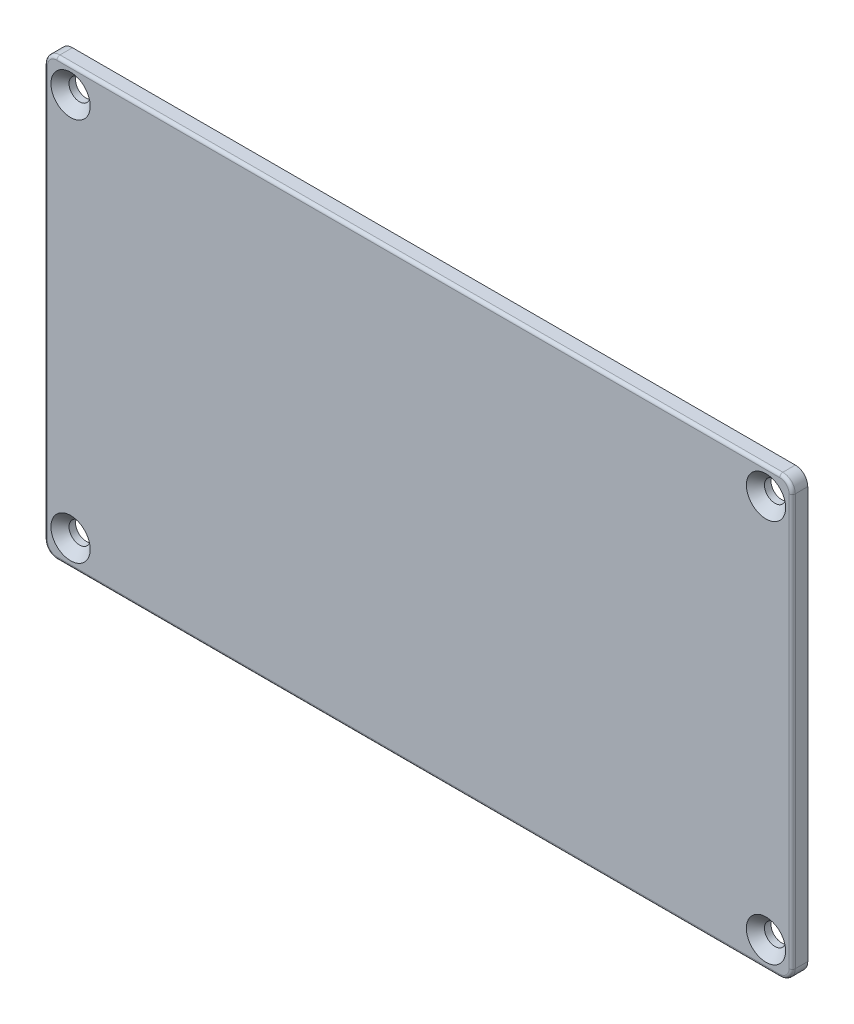
SolidWorks part; units mm, degrees
ref_plane "Front Plane" through (0, 0, 0) normal (0, 0, 1) x (1, 0, 0)
ref_plane "Top Plane" through (0, 0, 0) normal (0, 1, 0) x (1, 0, 0)
ref_plane "Right Plane" through (0, 0, 0) normal (1, 0, 0) x (0, 0, -1)
sketch "Sketch1" plane through (0, 0, 0) normal (0, 0, 1) x (1, 0, 0)
  line L1 (60, -35) -> (-60, -35)
  line L2 (60, -35) -> (60, 35)
  line L3 (60, 35) -> (-60, 35)
  line L4 (-60, -35) -> (-60, 35)
  line L5 (60, -35) -> (-60, 35) construction
  line L6 (60, 35) -> (-60, -35) construction
  point P0 (0, 0)
extrude "Boss-Extrude1" add sketch "Sketch1" along normal blind 2.5
fillet "Fillet1" radius 2 4 edges at (60, -35, 1.25) (-60, -35, 1.25) (-60, 35, 1.25) (60, 35, 1.25)
sketch "Sketch2" plane through (0, 0, 2.5) normal (0, 0, 1) x (1, 0, 0)
  line L0 (58, 35) -> (-58, 35) construction
  line L1 (-60, 33) -> (-60, -33) construction
  line L2 (-58, -35) -> (58, -35) construction
  line L3 (60, -33) -> (60, 33) construction
  circle A0 centre (-55.8, 30.8) radius 1.5
  circle A1 centre (55.8, 30.8) radius 1.5
  circle A2 centre (55.8, -30.8) radius 1.5
  circle A3 centre (-55.8, -30.8) radius 1.5
  dimension "D1" = 4.2
  dimension "D2" = 4.2
  dimension "D3" = 3
  dimension "D4" = 4.2
  dimension "D5" = 4.2
  dimension "D6" = 4.2
  dimension "D7" = 4.2
  dimension "D8" = 4.2
  dimension "D9" = 4.2
hole_wizard "CSK for M3 Countersunk Flat Head Screw1" positions "3DSketch1" profile "Sketch3" countersink size "M3" standard "ISO"
sketch3d "3DSketch1"
  point P0 (-55.8, 30.8, 2.5)
  point P3 (55.8, 30.8, 2.5)
  point P6 (55.8, -30.8, 2.5)
  point P9 (-55.8, -30.8, 2.5)
sketch "Sketch3" plane through (-55.8, 30.8, 2.5) normal (1, 0, 0) x (0, -1, 0)
  line L0 (0, 0) -> (0, 11.0215)
  line L1 (0, 11.0215) -> (1.7, 10)
  line L2 (1.7, 10) -> (1.7, 1.45)
  line L3 (1.7, 1.45) -> (3.15, 0)
  line L5 (3.15, 0) -> (0, 0)
  line L6 (-1.7, 1.45) -> (-3.15, 0) construction
  line L10 (0, 11.0215) -> (-1.7, 10) construction
  line L11 (0, -6.35) -> (0, 107.95) construction
  dimension "Hole Dia." = 3.4
  dimension "Hole Depth" = 10
  dimension "Near C'Sink Dia." = 6.3
  dimension "Near C'Sink Angle" = 90
  dimension "Drill Angle" = 118
fillet "Fillet2" radius 0.5 8 edges at (-59.4142, 34.4142, 2.5) (0, 35, 2.5) (59.4142, 34.4142, 2.5) (60, 0, 2.5) (59.4142, -34.4142, 2.5) (0, -35, 2.5) (-59.4142, -34.4142, 2.5) (-60, 0, 2.5)
